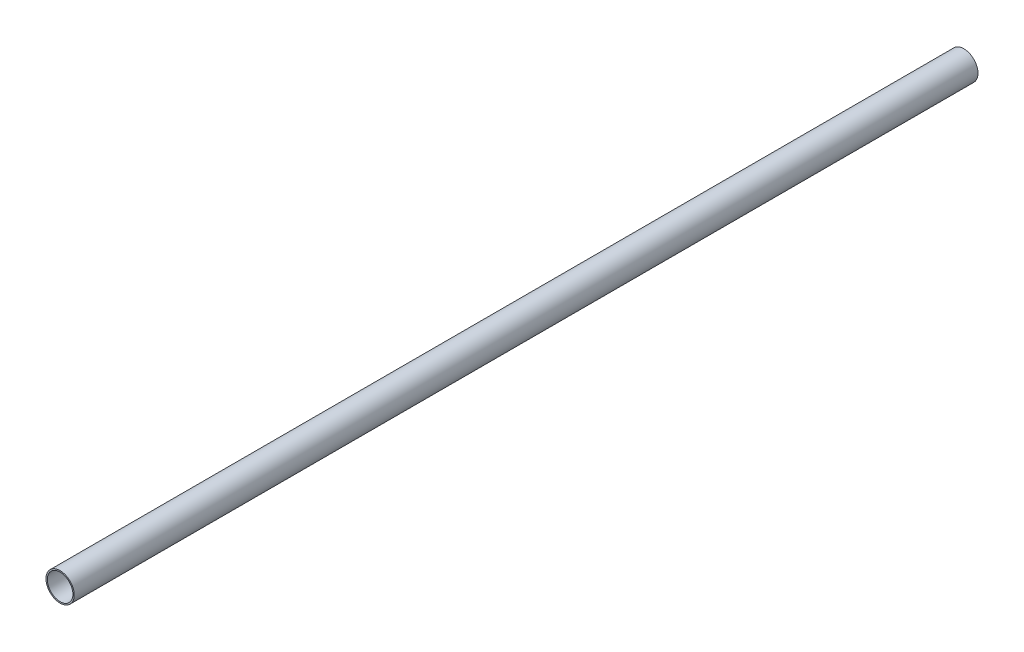
SolidWorks part; units mm, degrees
material "AISI 304"
ref_plane "Front Plane" through (0, 0, 0) normal (0, 0, 1) x (1, 0, 0)
ref_plane "Top Plane" through (0, 0, 0) normal (0, 1, 0) x (1, 0, 0)
ref_plane "Right Plane" through (0, 0, 0) normal (1, 0, 0) x (0, 0, -1)
sketch "Sketch1" plane through (0, 0, 0) normal (0, 0, 1) x (1, 0, 0)
  circle A0 centre (0, 0) radius 4.7625
  circle A1 centre (0, 0) radius 4.318
  dimension "D1" = 9.525
  dimension "D2" = 8.636
extrude "Boss-Extrude1" add sketch "Sketch1" along normal blind 304.8
